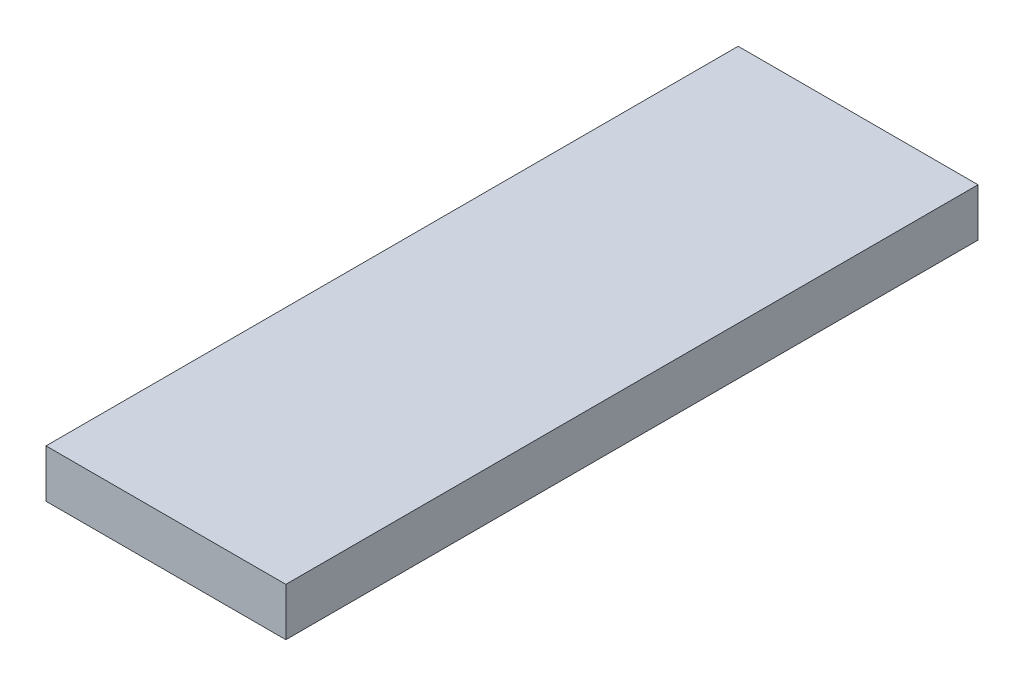
SolidWorks part; units mm, degrees
ref_plane "Front Plane" through (0, 0, 0) normal (0, 0, 1) x (1, 0, 0)
ref_plane "Top Plane" through (0, 0, 0) normal (0, 1, 0) x (1, 0, 0)
ref_plane "Right Plane" through (0, 0, 0) normal (1, 0, 0) x (0, 0, -1)
sketch "Sketch1" plane through (0, 0, 0) normal (0, 1, 0) x (1, 0, 0)
  line L1 (17.5, -50.5) -> (-17.5, -50.5)
  line L2 (17.5, -50.5) -> (17.5, 50.5)
  line L3 (17.5, 50.5) -> (-17.5, 50.5)
  line L4 (-17.5, -50.5) -> (-17.5, 50.5)
  line L5 (17.5, -50.5) -> (-17.5, 50.5) construction
  line L6 (17.5, 50.5) -> (-17.5, -50.5) construction
  point P0 (0, 0)
  dimension "D1" = 101
  dimension "D2" = 35
extrude "Boss-Extrude1" add sketch "Sketch1" along normal blind 7
